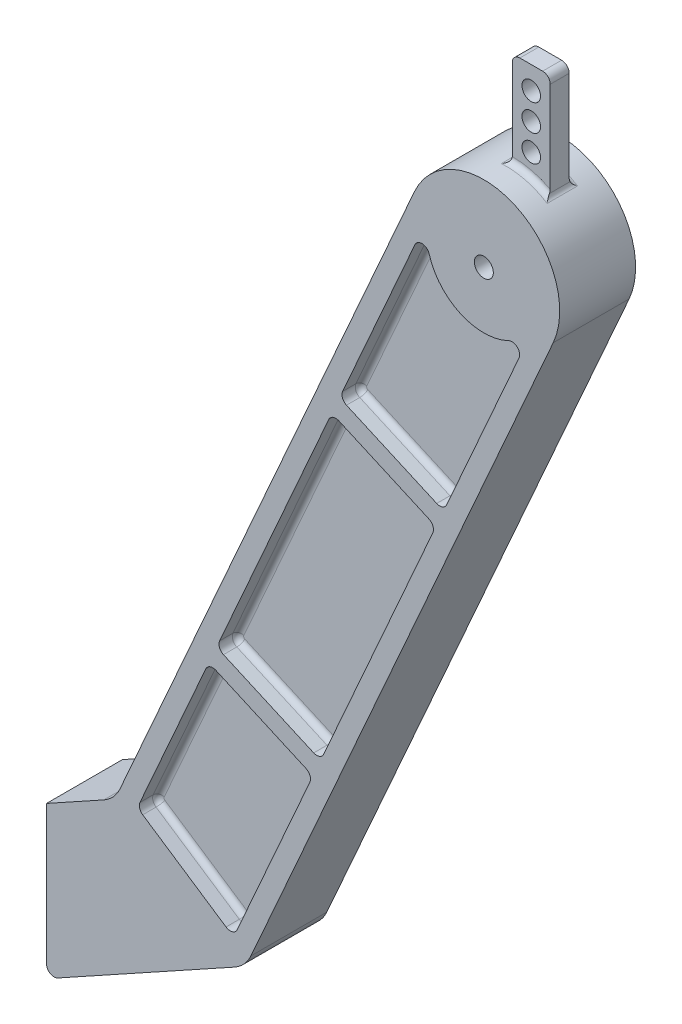
SolidWorks part; units mm, degrees
ref_plane "Front Plane" through (0, 0, 0) normal (0, 0, 1) x (1, 0, 0)
ref_plane "Top Plane" through (0, 0, 0) normal (0, 1, 0) x (1, 0, 0)
ref_plane "Right Plane" through (0, 0, 0) normal (1, 0, 0) x (0, 0, -1)
sketch "Sketch1" plane through (0, 0, 0) normal (0, 0, 1) x (1, 0, 0)
  line L0 (-23.2219, 10.291) -> (-121.7481, -212.0364)
  line L1 (-127.2106, -218.0034) -> (-146.3628, -228.6)
  line L2 (-146.3628, -228.6) -> (-146.3628, -275.0918)
  line L3 (-142.5931, -277.3143) -> (-83.4215, -244.5756)
  line L4 (-77.9589, -238.6086) -> (23.2219, -10.291)
  line L6 (0, 0) -> (0, -279.4) construction
  line L7 (-146.3628, -279.4) -> (0, -279.4) construction
  arc A0 (-23.2219, 10.291) -> (23.2219, -10.291) centre (0, 0) cw
  arc A1 (-83.4215, -244.5756) -> (-77.9589, -238.6086) centre (-89.5699, -233.4631) ccw
  arc A2 (-121.7481, -212.0364) -> (-127.2106, -218.0034) centre (-133.359, -206.8909) cw
  arc A3 (-146.3628, -275.0918) -> (-142.5931, -277.3143) centre (-143.8228, -275.0918) ccw
  circle A4 centre (0, 0) radius 3.175
  point P12 (-79.6878, -242.5098)
  dimension "D1" = 25.4
  dimension "D7" = 12.7
  dimension "D8" = 2.54
  dimension "D9" = 6.35
  dimension "D2" = 44.45
  dimension "D3" = 254
  dimension "D4" = 279.4
  dimension "D5" = 76.2
  dimension "D6" = 50.8
extrude "Boss-Extrude1" add sketch "Sketch1" along normal mid plane 25.4
sketch "Sketch2" plane through (0, 0, 12.7) normal (0, 0, 1) x (1, 0, 0)
  line L0 (-87.131, -155.8641) -> (-56.9425, -169.2423)
  line L1 (-45.9671, -62.9765) -> (-15.7787, -76.3548)
  line L2 (-48.5399, -68.782) -> (-18.3514, -82.1603)
  line L3 (-89.7037, -161.6696) -> (-59.5153, -175.0478)
  line L4 (-51.8911, -70.0751) -> (-88.4241, -152.5128)
  line L5 (-12.4274, -75.0617) -> (11.7798, -20.4374)
  line L6 (-17.4164, 7.7182) -> (-115.9426, -214.6092)
  line L7 (-23.053, -5.0009) -> (-47.2602, -59.6252)
  line L8 (-114.161, -215.7955) -> (-86.2732, -234.3653)
  line L9 (-83.7644, -236.0359) -> (17.4164, -7.7182)
  line L10 (-82.5432, -233.2803) -> (-58.2222, -178.3991)
  line L11 (-93.055, -162.9626) -> (-115.0754, -212.6522)
  line L12 (-53.5912, -167.9492) -> (-17.0583, -85.5115)
  line L13 (-48.2893, -61.9474) -> (-13.4565, -77.3839) construction
  line L14 (-50.8621, -67.7529) -> (-16.0292, -83.1894) construction
  line L15 (-89.4532, -154.835) -> (-54.6203, -170.2714) construction
  line L16 (-92.0259, -160.6405) -> (-57.1931, -176.0769) construction
  arc A0 (-18.2919, -5.3206) -> (8.345, -17.125) centre (0, 0) ccw
  arc A1 (-115.0754, -212.6522) -> (-114.161, -215.7955) centre (-112.7532, -213.6813) ccw
  arc A2 (11.7798, -20.4374) -> (8.345, -17.125) centre (9.4576, -19.4083) ccw
  arc A3 (-82.5432, -233.2803) -> (-86.2732, -234.3653) centre (-84.8654, -232.2512) cw
  arc A4 (-23.053, -5.0009) -> (-18.2919, -5.3206) centre (-20.7308, -6.03) cw
  arc A5 (-45.9671, -62.9765) -> (-47.2602, -59.6252) centre (-44.938, -60.6543) cw
  arc A6 (-15.7787, -76.3548) -> (-12.4274, -75.0617) centre (-14.7496, -74.0326) ccw
  arc A7 (-48.5399, -68.782) -> (-51.8911, -70.0751) centre (-49.569, -71.1042) ccw
  arc A8 (-18.3514, -82.1603) -> (-17.0583, -85.5115) centre (-19.3805, -84.4824) cw
  arc A9 (-56.9425, -169.2423) -> (-53.5912, -167.9492) centre (-55.9134, -166.9201) ccw
  arc A10 (-87.131, -155.8641) -> (-88.4241, -152.5128) centre (-86.1019, -153.5419) cw
  arc A11 (-59.5153, -175.0478) -> (-58.2222, -178.3991) centre (-60.5444, -177.37) cw
  arc A12 (-89.7037, -161.6696) -> (-93.055, -162.9626) centre (-90.7328, -163.9917) ccw
  point P41 (-54.6203, -170.2714)
  dimension "D3" = 2.54
  dimension "D4" = 2.54
  dimension "D5" = 2.54
  dimension "D10" = 2.54
  dimension "D6" = 76.2
  dimension "D7" = 177.8
  dimension "D8" = 6.35
  dimension "D1" = 6.35
  dimension "D2" = 6.35
  dimension "D9" = 6.35
extrude "Cut-Extrude1" cut sketch "Sketch2" against normal blind 6.35
mirror "Mirror1" about plane through (0, 0, 0) normal (0, 0, 1) of "Cut-Extrude1"
sketch "Sketch3" plane through (0, 0, 0) normal (0, 0, 1) x (1, 0, 0)
  line L0 (0, 0) -> (0, 57.15) construction
  line L1 (6.35, 57.15) -> (6.35, 24.5934) construction
  line L3 (0, 25.4) -> (0, 54.61)
  line L4 (2.54, 57.15) -> (10.16, 57.15)
  line L5 (12.7, 21.997) -> (12.7, 54.61)
  arc A0 (12.7, 21.997) -> (0, 25.4) centre (0, 0) ccw
  arc A1 (23.2219, -10.291) -> (-23.2219, 10.291) centre (0, 0) ccw construction
  arc A2 (10.16, 57.15) -> (12.7, 54.61) centre (10.16, 54.61) cw
  arc A3 (2.54, 57.15) -> (0, 54.61) centre (2.54, 54.61) ccw
  circle A4 centre (6.35, 49.53) radius 3.1115
  circle A5 centre (6.35, 40.64) radius 3.1115
  circle A6 centre (6.35, 31.75) radius 3.1115
  point P13 (12.7, 57.15)
  dimension "D3" = 2.54
  dimension "D4" = 6.223
  dimension "D5" = 6.223
  dimension "D6" = 6.223
  dimension "D1" = 12.7
  dimension "D2" = 31.75
  dimension "D7" = 7.62
  dimension "D8" = 8.89
  dimension "D9" = 8.89
extrude "Boss-Extrude2" add sketch "Sketch3" along normal mid plane 6.35
fillet "Fillet1" radius 1.905 4 edges at (0, 25.4, 0) (6.574, 24.5345, -3.175) (12.7, 21.997, 0) (6.574, 24.5345, 3.175)
fillet "Fillet2" radius 1.905 48 edges at (-7.7182, -17.4164, -6.35) (-20.5607, -3.4957, -6.35) (-35.1566, -32.3131, -6.35) (-47.3077, -61.5687, -6.35) (-30.8729, -69.6657, -6.35) (-13.8352, -76.4023, -6.35) (-0.3238, -47.7495, -6.35) (11.2208, -17.5799, -6.35) (-70.1576, -111.2939, -6.35) (-88.4716, -154.4562, -6.35) (-72.0368, -162.5532, -6.35) (-54.9991, -169.2899, -6.35) (-35.3248, -126.7304, -6.35) (-17.0108, -83.5681, -6.35) (-33.4456, -75.4711, -6.35) (-50.4833, -68.7345, -6.35) (-100.2171, -225.0804, -6.35) (-84.1559, -234.6901, -6.35) (-70.3827, -205.8397, -6.35) (-58.1747, -176.4556, -6.35) (-74.6095, -168.3587, -6.35) (-91.6472, -161.622, -6.35) (-104.0652, -187.8074, -6.35) (-115.1921, -214.3908, -6.35) (-33.4456, -75.4711, 6.35) (-17.0108, -83.5681, 6.35) (-35.3248, -126.7304, 6.35) (-54.9991, -169.2899, 6.35) (-72.0368, -162.5532, 6.35) (-88.4716, -154.4562, 6.35) (-70.1576, -111.2939, 6.35) (-50.4833, -68.7345, 6.35) (-104.0652, -187.8074, 6.35) (-91.6472, -161.622, 6.35) (-74.6095, -168.3587, 6.35) (-58.1747, -176.4556, 6.35) (-70.3827, -205.8397, 6.35) (-84.1559, -234.6901, 6.35) (-100.2171, -225.0804, 6.35) (-115.1921, -214.3908, 6.35) (-0.3238, -47.7495, 6.35) (-13.8352, -76.4023, 6.35) (-30.8729, -69.6657, 6.35) (-47.3077, -61.5687, 6.35) (-35.1566, -32.3131, 6.35) (-20.5607, -3.4957, 6.35) (-7.7182, -17.4164, 6.35) (11.2208, -17.5799, 6.35)
